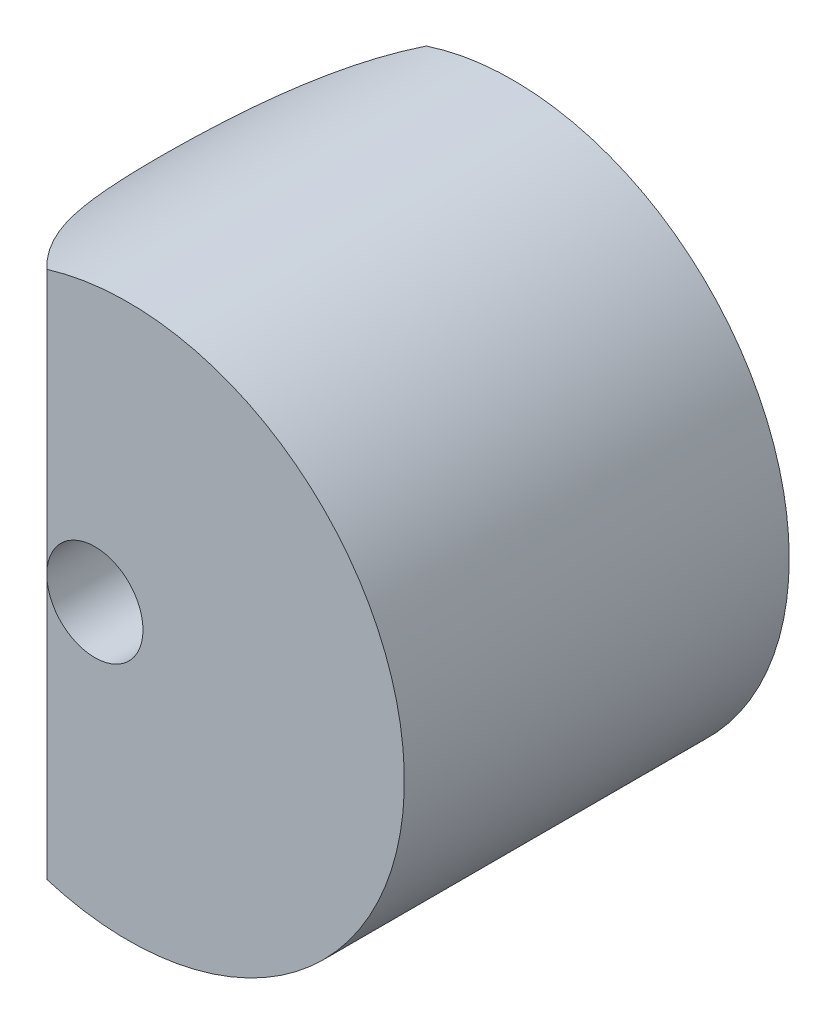
SolidWorks part; units mm, degrees
ref_plane "Front Plane" through (0, 0, 0) normal (0, 0, 1) x (1, 0, 0)
ref_plane "Top Plane" through (0, 0, 0) normal (0, 1, 0) x (1, 0, 0)
ref_plane "Right Plane" through (0, 0, 0) normal (1, 0, 0) x (0, 0, -1)
sketch "Sketch1" plane through (0, 0, 0) normal (0, 1, 0) x (1, 0, 0)
  line L1 (0, -40) -> (57.45, -40)
  line L2 (0, -40) -> (0, 40)
  line L3 (0, 40) -> (57.45, 40)
  line L4 (57.45, -40) -> (57.45, 40)
  point P4 (0, 0)
  dimension "D1" = 57.45
  dimension "D2" = 80
revolve "Revolve2" add sketch "Sketch1" angle 360 about L2
sketch "Sketch2" plane through (0, 0, 0) normal (0, 1, 0) x (1, 0, 0)
  line L2 (-57.45, -40) -> (57.45, -40) construction
  line L3 (-57.45, 40) -> (-16.8823, 40)
  line L4 (-57.45, 40) -> (-57.45, -40)
  line L5 (-57.45, -40) -> (-16.8823, -40)
  arc A0 (-16.8823, -40) -> (-16.8823, 41.1242) centre (22.5496, 0.5621) cw
  point P3 (0, 0)
  point P4 (0, 0)
  point P12 (0, 0)
  dimension "D1" = 56.57
extrude "Cut-Extrude1" cut sketch "Sketch2" against normal through all and the other way through all contours L5 A0 L3 L4
sketch "Sketch3" plane through (0, 0, 40) normal (0, 0, 1) x (1, 0, 0)
  line L0 (-16.8823, 0) -> (-6.8823, 0)
  line L1 (-16.8823, -54.9135) -> (-16.8823, 54.9135) construction
  circle A1 centre (-6.8823, 0) radius 10
  dimension "D1" = 10
extrude "Cut-Extrude3" cut sketch "Sketch3" against normal through all
